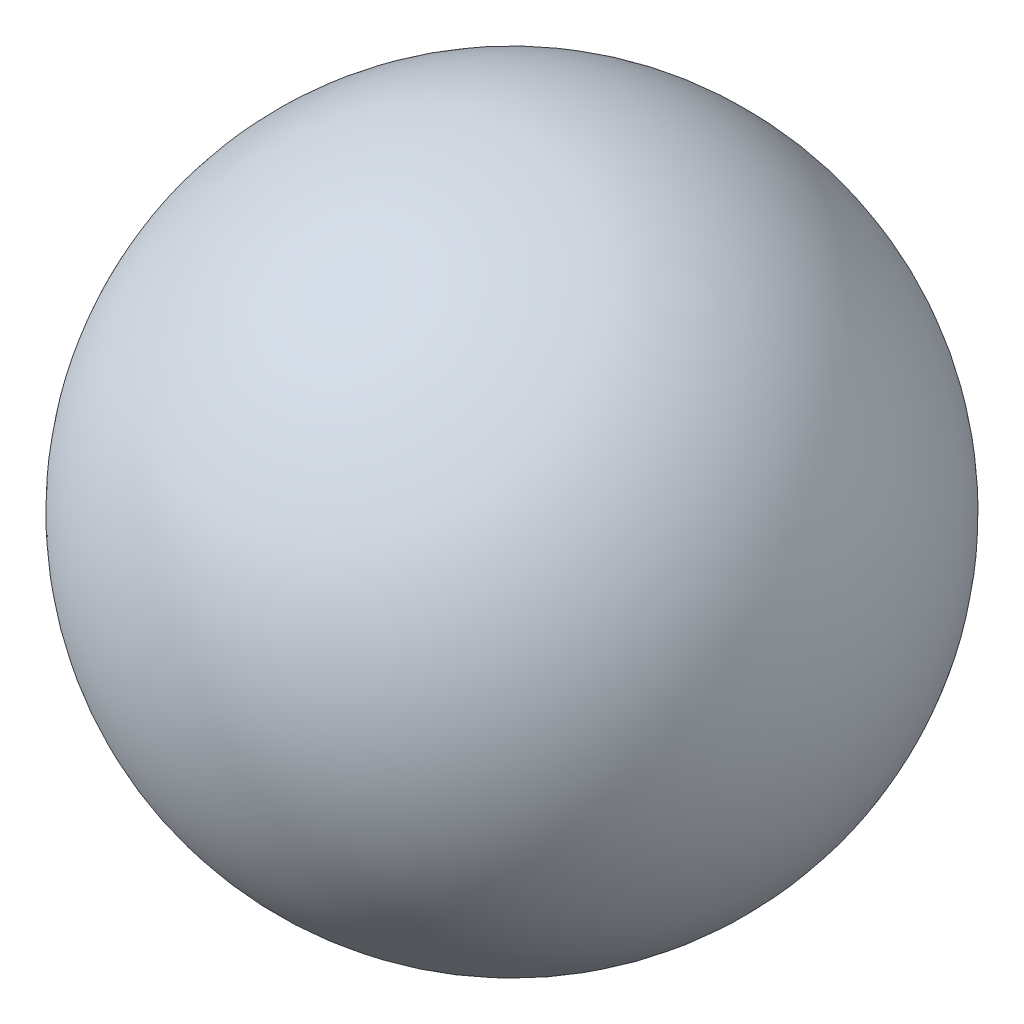
SolidWorks part; units mm, degrees
material "Легированная сталь"
ref_plane "Спереди" through (0, 0, 0) normal (0, 0, 1) x (1, 0, 0)
ref_plane "Сверху" through (0, 0, 0) normal (0, 1, 0) x (1, 0, 0)
ref_plane "Справа" through (0, 0, 0) normal (1, 0, 0) x (0, 0, -1)
sketch "Эскиз1" plane through (0, 0, 0) normal (0, 0, 1) x (1, 0, 0)
  line L1 (-0.6, 0) -> (0.6, 0)
  arc A1 (0.6, 0) -> (-0.6, 0) centre (0, 0) ccw
  dimension "D1" = 1.2
revolve "Повернуть1" add sketch "Эскиз1" angle 360 about L1
